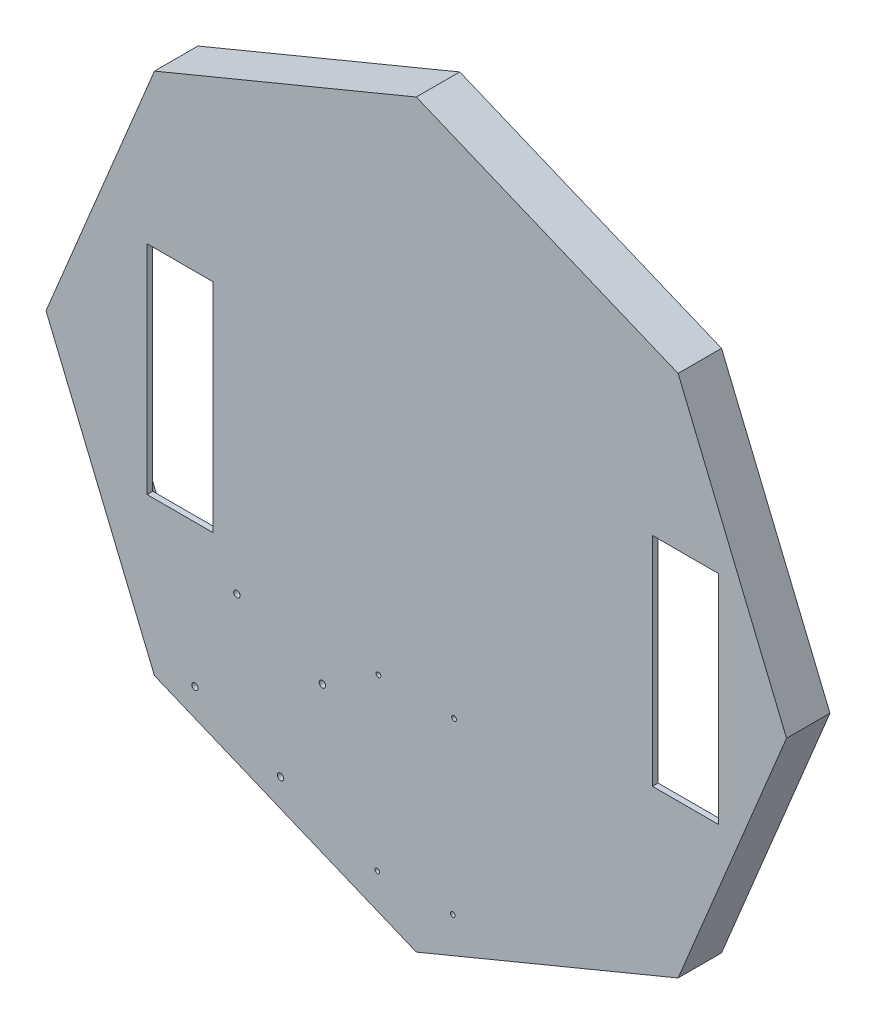
SolidWorks part; units mm, degrees
ref_plane "Front Plane" through (0, 0, 0) normal (0, 0, 1) x (1, 0, 0)
ref_plane "Top Plane" through (0, 0, 0) normal (0, 1, 0) x (1, 0, 0)
ref_plane "Right Plane" through (0, 0, 0) normal (1, 0, 0) x (0, 0, -1)
sketch "Sketch1" plane through (0, 0, 0) normal (0, 0, 1) x (1, 0, 0)
  line L0 (0, 0) -> (0, -195.9844) construction
  line L1 (0, 0) -> (-138.5819, -138.5819) construction
  line L2 (0, 0) -> (-195.9844, 0) construction
  line L3 (0, 0) -> (-138.5819, 138.5819) construction
  line L4 (0, 0) -> (0, 195.9844) construction
  line L5 (0, 0) -> (138.5819, 138.5819) construction
  line L6 (0, 0) -> (195.9844, 0) construction
  line L7 (0, 0) -> (138.5819, -138.5819) construction
  line L8 (0, 195.9844) -> (-138.5819, 138.5819)
  line L9 (-138.5819, 138.5819) -> (-195.9844, 0)
  line L10 (-195.9844, 0) -> (-138.5819, -138.5819)
  line L11 (-138.5819, -138.5819) -> (0, -195.9844)
  line L12 (0, -195.9844) -> (138.5819, -138.5819)
  line L13 (138.5819, -138.5819) -> (195.9844, 0)
  line L14 (195.9844, 0) -> (138.5819, 138.5819)
  line L15 (138.5819, 138.5819) -> (0, 195.9844)
  circle A0 centre (0, 0) radius 195.9844 construction
  point P13 (0, 0)
  dimension "D2" = 150
  dimension "D1" = 8
extrude "Boss-Extrude1" add sketch "Sketch1" along normal blind 3
sketch "Sketch5" plane through (-69.291, -167.2832, 0) normal (-0.3827, -0.9239, 0) x (0.9239, -0.3827, 0)
  line L1 (75, 0) -> (75, -20)
  line L2 (-75, 0) -> (-75, -20)
  line L3 (75, -20) -> (-75, -20)
  line L4 (-125, 35.4266) -> (-75, -20) construction
  line L5 (-125, 35.4266) -> (75, -20) construction
  line L6 (75, 0) -> (-75, 0)
  line L7 (-75, 3) -> (-75, 0) construction
  line L8 (-75, 0) -> (75, 0) construction
  line L9 (75, 3) -> (75, 0) construction
  point P1 (-125, 35.4266)
  dimension "D1" = 20
  dimension "D2" = 20
extrude "Boss-Extrude2" add sketch "Sketch5" against normal blind 3
mirror "Mirror1" about plane through (0, 0, 0) normal (0, 1, 0) of "Boss-Extrude2"
mirror "Mirror2" about plane through (0, 0, 0) normal (1, 0, 0) of "Mirror1", "Boss-Extrude2"
sketch "Sketch6" plane through (-167.2832, -69.291, 0) normal (-0.9239, -0.3827, 0) x (0, 0, 1)
  line L0 (3, 75) -> (0, 75) construction
  line L1 (3, -75) -> (-20, -75)
  line L2 (3, -75) -> (3, 75)
  line L3 (3, 75) -> (-20, 75)
  line L4 (-20, -75) -> (-20, 75)
  dimension "D1" = 23
extrude "Boss-Extrude3" add sketch "Sketch6" against normal blind 3
mirror "Mirror3" about plane through (0, 0, 0) normal (0, 1, 0) of "Boss-Extrude3"
mirror "Mirror4" about plane through (0, 0, 0) normal (1, 0, 0) of "Boss-Extrude1", "Mirror3"
fillet "Fillet1" radius 2 8 edges at (68.1429, 164.5115, 0) (-68.1429, 164.5115, 0) (-164.5115, 68.1429, 0) (-164.5115, -68.1429, 0) (-68.1429, -164.5115, 0) (68.1429, -164.5115, 0) (164.5115, 68.1429, 0) (164.5115, -68.1429, 0)
sketch "Sketch4" plane through (0, 0, 0) normal (0, 0, -1) x (-1, 0, 0)
  line L1 (-125, 57.5) -> (-160, 57.5)
  line L2 (-125, 57.5) -> (-125, -57.5)
  line L3 (-125, -57.5) -> (-160, -57.5)
  line L4 (-160, 57.5) -> (-160, -57.5)
  line L5 (-125, 57.5) -> (-160, -57.5) construction
  line L6 (-125, -57.5) -> (-160, 57.5) construction
  line L7 (107.5, 57.5) -> (142.5, 57.5)
  line L8 (107.5, 57.5) -> (107.5, -57.5)
  line L9 (107.5, -57.5) -> (142.5, -57.5)
  line L10 (142.5, 57.5) -> (142.5, -57.5)
  line L11 (107.5, 57.5) -> (142.5, -57.5) construction
  line L12 (107.5, -57.5) -> (142.5, 57.5) construction
  point P0 (-142.5, 0)
  point P5 (125, 0)
  dimension "D1" = 115
  dimension "D2" = 115
  dimension "D3" = 35
  dimension "D4" = 35
  dimension "D5" = 125
  dimension "D6" = 125
extrude "Cut-Extrude1" cut sketch "Sketch4" against normal blind 10
sketch "Sketch7" plane through (0, 0, 0) normal (0, 0, -1) x (-1, 0, 0)
  line L0 (-22, -165.9844) -> (22, -165.9844)
  line L1 (-22, -165.9844) -> (-22, -156.9844)
  line L2 (-22, -156.9844) -> (-25, -156.9844)
  line L3 (-25, -156.9844) -> (-25, -171.9844)
  line L4 (-25, -171.9844) -> (25, -171.9844)
  line L5 (25, -171.9844) -> (25, -156.9844)
  line L6 (25, -156.9844) -> (22, -156.9844)
  line L7 (22, -156.9844) -> (22, -165.9844)
  dimension "D1" = 44
  dimension "D2" = 22
  dimension "D3" = 6
  dimension "D4" = 30
  dimension "D5" = 3
  dimension "D6" = 15
extrude "Boss-Extrude4" [suppressed] add sketch "Sketch7" along normal blind 5
hole_wizard "Tap Drill for M3 Tap1" [suppressed] positions "Sketch9" profile "Sketch10" hole size "M3" standard "ISO"
sketch "Sketch9" [suppressed] plane through (0, 0, -5) normal (0, 0, -1) x (-1, 0, 0)
  line L0 (-25, -156.9844) -> (-25, -171.9844) construction
  line L1 (25, -171.9844) -> (25, -156.9844) construction
  point P0 (-20, -169.0413)
  point P2 (20, -169.0413)
  dimension "D1" = 5
  dimension "5" = 5
sketch "Sketch10" plane through (20, -169.0413, -5) normal (1, 0, 0) x (0, 1, 0)
  line L0 (0, 0) -> (0, 8)
  line L1 (0, 8) -> (1.25, 8)
  line L2 (1.25, 8) -> (1.25, 0)
  line L5 (1.25, 0) -> (0, 0)
  line L11 (0, -6.35) -> (0, 107.95) construction
  dimension "Thru Hole Dia." = 2.5
  dimension "Thru Hole Depth" = 8
sketch "Sketch11" [suppressed] plane through (0, 0, 0) normal (0, 0, -1) x (-1, 0, 0)
  line L0 (22, -156.9844) -> (22, -165.9844) construction
  line L1 (25, -156.9844) -> (22, -156.9844) construction
  line L2 (25, -171.9844) -> (25, -156.9844) construction
  line L3 (-25, -171.9844) -> (25, -171.9844) construction
  line L4 (-25, -156.9844) -> (-25, -171.9844) construction
  line L5 (-22, -156.9844) -> (-25, -156.9844) construction
  line L6 (-22, -165.9844) -> (-22, -156.9844) construction
  line L7 (22, -165.9844) -> (-22, -165.9844) construction
  line L8 (22, -156.9844) -> (22, -165.9844)
  line L9 (25, -156.9844) -> (22, -156.9844)
  line L10 (25, -171.9844) -> (25, -156.9844)
  line L11 (-25, -171.9844) -> (25, -171.9844)
  line L12 (-25, -156.9844) -> (-25, -171.9844)
  line L13 (-22, -156.9844) -> (-25, -156.9844)
  line L14 (-22, -165.9844) -> (-22, -156.9844)
  line L15 (22, -165.9844) -> (-22, -165.9844)
hole_wizard "Tap Drill for M3 Tap2" positions "Sketch12" profile "Sketch13" hole size "M3" standard "ISO" end condition through all
sketch "Sketch12" plane through (0, 0, 0) normal (0, 0, -1) x (-1, 0, 0)
  point P0 (-19.3434, -169.0629)
  point P2 (20.6285, -169.0786)
sketch "Sketch13" plane through (19.3434, -169.0629, 0) normal (1, 0, 0) x (0, 1, 0)
  line L0 (0, 0) -> (0, 3)
  line L1 (0, 3) -> (1.25, 3)
  line L2 (1.25, 3) -> (1.25, 0)
  line L5 (1.25, 0) -> (0, 0)
  line L11 (0, -6.35) -> (0, 107.95) construction
  dimension "Thru Hole Dia." = 2.5
  dimension "Thru Hole Depth" = 3
hole_wizard "Tap Drill for M3 Tap3" positions "Sketch14" profile "Sketch15" hole size "M3" standard "ISO" end condition through all
sketch "Sketch14" plane through (0, 0, 0) normal (0, 0, -1) x (-1, 0, 0)
  point P0 (-20, -78.8903)
  point P3 (20, -78.8903)
sketch "Sketch15" plane through (20, -78.8903, 0) normal (1, 0, 0) x (0, 1, 0)
  line L0 (0, 0) -> (0, 3)
  line L1 (0, 3) -> (1.25, 3)
  line L2 (1.25, 3) -> (1.25, 0)
  line L5 (1.25, 0) -> (0, 0)
  line L11 (0, -6.35) -> (0, 107.95) construction
  dimension "Thru Hole Dia." = 2.5
  dimension "Thru Hole Depth" = 3
hole_wizard "M3 Clearance Hole1" positions "Sketch18" profile "Sketch17" hole size "M3" standard "ISO" end condition through all
sketch "Sketch18" plane through (0, 0, 3) normal (0, 0, 1) x (1, 0, 0)
  point P0 (-49.6806, -98.015)
  point P3 (-71.8762, -151.6)
  point P9 (-94.9507, -79.2635)
  point P14 (-117.1463, -132.8486)
sketch "Sketch17" plane through (-49.6806, -98.015, 3) normal (1, 0, 0) x (0, -1, 0)
  line L0 (0, 0) -> (0, 23)
  line L1 (0, 23) -> (1.7, 23)
  line L2 (1.7, 23) -> (1.7, 0)
  line L5 (1.7, 0) -> (0, 0)
  line L11 (0, -6.35) -> (0, 107.95) construction
  dimension "Thru Hole Dia." = 3.4
  dimension "Thru Hole Depth" = 23
sketch "Sketch21" plane through (0, 0, 0) normal (0, 0, -1) x (-1, 0, 0)
  line L1 (0, -195.9844) -> (-50.931, -174.8881)
  line L6 (49.5354, -175.4662) -> (0, -195.9844)
  line L7 (-50.931, -174.8881) -> (49.5354, -175.4662)
